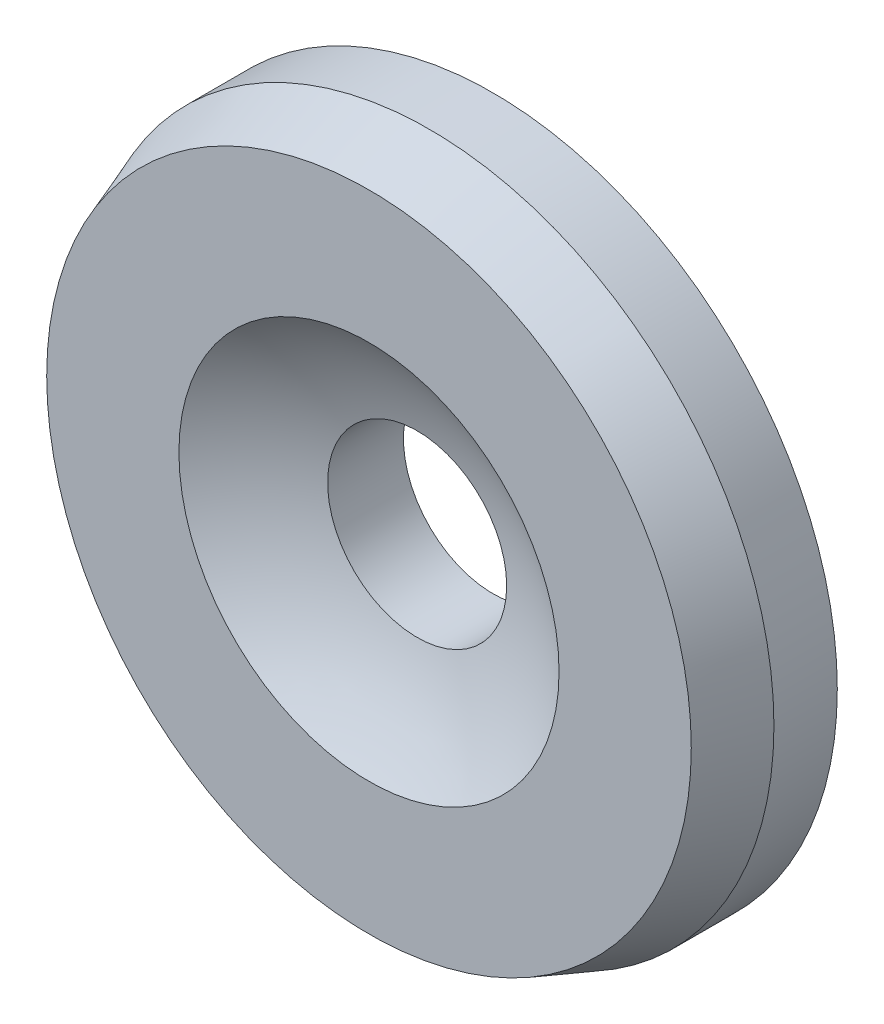
SolidWorks part; units mm, degrees
ref_plane "Alzado" through (0, 0, 0) normal (0, 0, 1) x (1, 0, 0)
ref_plane "Planta" through (0, 0, 0) normal (0, 1, 0) x (1, 0, 0)
ref_plane "Vista lateral" through (0, 0, 0) normal (1, 0, 0) x (0, 0, -1)
sketch "Sketch1" plane through (0, 0, 0) normal (0, 1, 0) x (1, 0, 0)
  line L0 (1.25, -1.55) -> (1.25, -1.32)
  line L1 (1.25, -1.32) -> (0.325, -1.32)
  line L2 (0.325, -1.32) -> (0.325, -1.5952)
  line L3 (0.69, -1.77) -> (1.1699, -1.77)
  line L4 (1.1699, -1.77) -> (1.25, -1.55)
  line L5 (0, -1.32) -> (0, -1.77) construction
  arc A0 (0.325, -1.5952) -> (0.69, -1.77) centre (0, -2.742) cw
  dimension "D1" = 1.192
  dimension "D2" = 0.325
  dimension "D3" = 0.69
  dimension "D4" = 1.1699
  dimension "D5" = 1.25
  dimension "D6" = 0.23
  dimension "D7" = 0.2752
revolve "Revolve1" add sketch "Sketch1" angle 360 about L5
